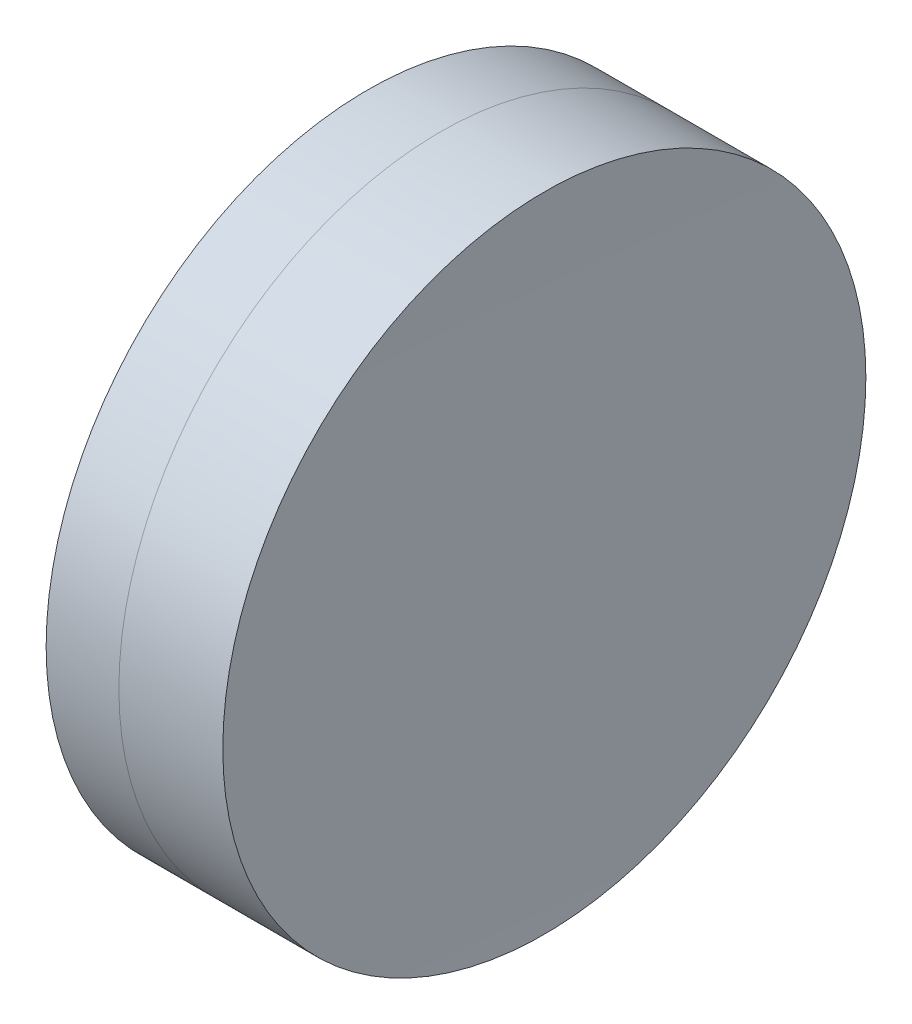
SolidWorks part; units mm, degrees
ref_plane "前视基准面" through (0, 0, 0) normal (0, 0, 1) x (1, 0, 0)
ref_plane "上视基准面" through (0, 0, 0) normal (0, 1, 0) x (1, 0, 0)
ref_plane "右视基准面" through (0, 0, 0) normal (1, 0, 0) x (0, 0, -1)
sketch "草图1" plane through (0, 0, 0) normal (0, 1, 0) x (1, 0, 0)
  line L0 (124.5233, 0) -> (646.9917, 0) construction
  line L1 (299.1702, -6.35) -> (300.6068, -6.35)
  line L2 (299.1702, 6.35) -> (300.6068, 6.35)
  arc A0 (300.6068, -6.35) -> (300.6068, 6.35) centre (260.709, 0) ccw
  arc A1 (299.1702, 6.35) -> (299.1702, -6.35) centre (334.809, 0) ccw
  point P10 (298.609, 0)
  point P11 (301.109, 0)
  dimension "D3" = 36.2
  dimension "D4" = 40.4
  dimension "D1" = 6.35
  dimension "D2" = 6.35
  dimension "D5" = 2.5
revolve "旋转1" add sketch "草图1" angle 360 about L0
sketch "草图2" plane through (0, 0, 0) normal (0, 1, 0) x (1, 0, 0)
  line L0 (-0.5519, 0) -> (622.6607, 0) construction
  line L2 (300.6068, 6.35) -> (302.6596, 6.35)
  line L3 (300.6068, -6.35) -> (302.6596, -6.35)
  arc A0 (302.6596, 6.35) -> (302.6596, -6.35) centre (700.709, 0) ccw
  arc A1 (300.6068, -6.35) -> (300.6068, 6.35) centre (260.709, 0) ccw construction
  arc A2 (300.6068, -6.35) -> (300.6068, 6.35) centre (260.709, 0) ccw
  point P8 (302.609, 0)
  point P12 (301.109, 0)
  dimension "D1" = 398.1
  dimension "D2" = 1.5
revolve "旋转3" add sketch "草图2" angle 360 about L0
